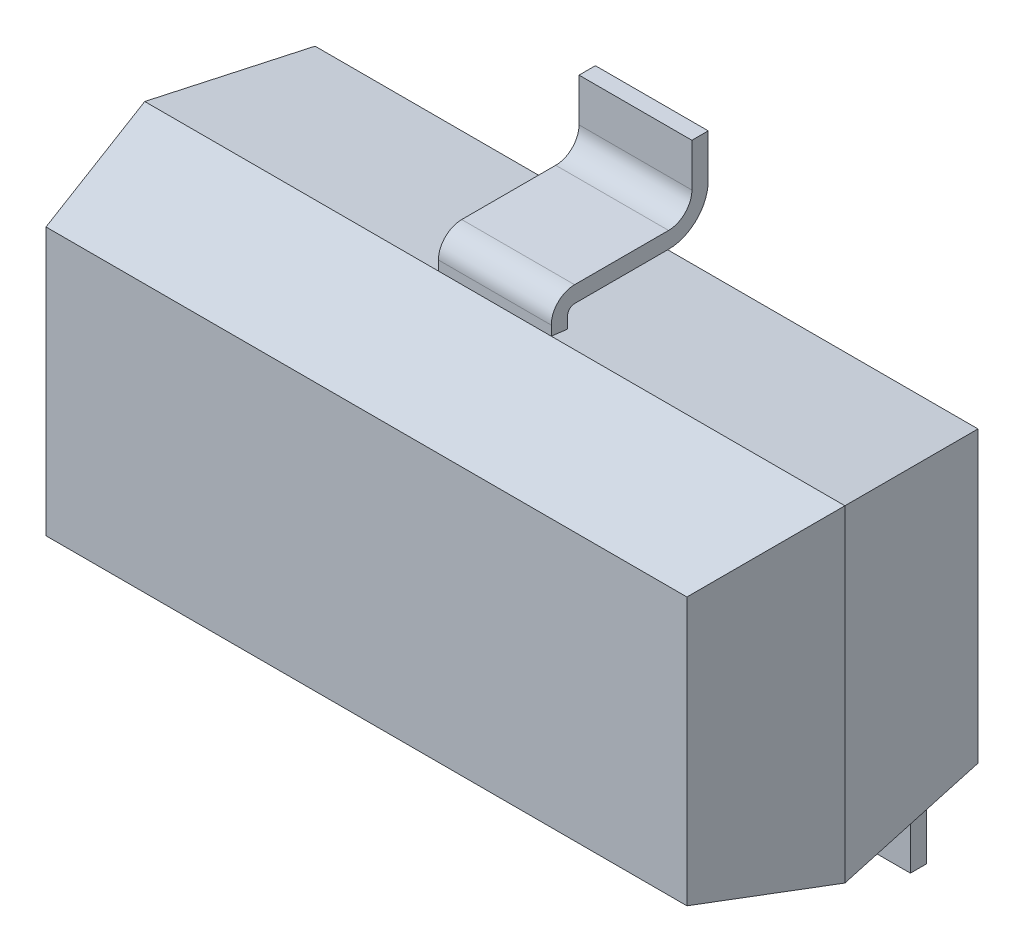
SolidWorks part; units mm, degrees
material "-"
ref_plane "Alzado" through (0, 0, 0) normal (0, 0, 1) x (1, 0, 0)
ref_plane "Planta" through (0, 0, 0) normal (0, 1, 0) x (1, 0, 0)
ref_plane "Vista lateral" through (0, 0, 0) normal (1, 0, 0) x (0, 0, -1)
sketch "Croquis1" plane through (0, 0, 0) normal (0, 0, 1) x (1, 0, 0)
  line L1 (1.5, 0.7) -> (-1.5, 0.7)
  line L2 (1.5, 0.7) -> (1.5, -0.7)
  line L3 (1.5, -0.7) -> (-1.5, -0.7)
  line L4 (-1.5, 0.7) -> (-1.5, -0.7)
  line L5 (1.5, 0.7) -> (-1.5, -0.7) construction
  line L6 (1.5, -0.7) -> (-1.5, 0.7) construction
  point P0 (0, 0)
  dimension "D1" = 1.4
  dimension "D2" = 3
extrude "Saliente-Extruir1" add sketch "Croquis1" along normal blind 0.55 draft 13 and the other way blind 0.65 draft 7
sketch "Croquis5" plane through (0, 0, 0) normal (0, 0, 1) x (1, 0, 0)
  line L0 (0, 1.2725) -> (0, 0) construction
  line L1 (0.6945, 0.573) -> (-0.7455, 0.573) construction
  line L2 (0, 0) -> (0, -1.0302) construction
  line L3 (0, -0.573) -> (-0.9362, -0.573) construction
  line L4 (-1.373, -0.573) -> (1.373, -0.573) construction
  line L5 (-0.9362, -0.573) -> (-0.9362, -1.0302) construction
  line L6 (-0.9362, -1.0302) -> (-0.6945, -1.0302) construction
  line L7 (-0.9362, -1.0302) -> (-1.178, -1.0302) construction
  line L8 (-1.178, -1.0302) -> (-1.178, -0.573) construction
  line L9 (-1.178, -0.573) -> (-0.6945, -0.573) construction
  line L10 (-0.6945, -0.573) -> (-0.6945, -1.0302) construction
  line L11 (-0.6945, -1.0302) -> (-0.6945, -0.573) construction
  line L12 (-0.9362, -0.573) -> (-0.9362, -1.1257) construction
  line L13 (-0.9362, -1.1257) -> (-0.6945, -1.1257) construction
  line L14 (-0.6945, -1.1257) -> (-0.6945, -1.0302) construction
  line L15 (-0.6945, -1.0302) -> (-1.178, -1.0302) construction
  line L16 (-1.178, -1.0302) -> (-1.178, -1.1257) construction
  line L17 (-1.178, -1.1257) -> (-0.9362, -1.1257) construction
  line L18 (-0.6945, -1.1257) -> (-0.6945, -0.7474) construction
  line L19 (-0.6945, -0.7474) -> (-1.178, -0.7474) construction
  line L20 (1.373, 0.573) -> (-1.373, 0.573) construction
  line L21 (-1.178, -0.573) -> (-0.6945, -0.573)
  line L23 (-0.6945, -0.573) -> (-0.6945, -1.1257)
  line L25 (-0.6945, -1.1257) -> (-1.178, -1.1257)
  line L26 (-1.178, -1.1257) -> (-1.178, -0.573)
  line L27 (1.178, -1.1257) -> (1.178, -0.573)
  line L28 (1.178, -0.573) -> (0.6945, -0.573)
  line L29 (0.6945, -0.573) -> (0.6945, -1.1257)
  line L30 (0.6945, -1.1257) -> (1.178, -1.1257)
  line L31 (0.2418, 0.573) -> (0.2418, 1.1257)
  line L32 (0.2418, 1.1257) -> (-0.2418, 1.1257)
  line L33 (-0.2418, 1.1257) -> (-0.2418, 0.573)
  line L34 (-0.2418, 0.573) -> (0.2418, 0.573)
  line L35 (-1.5, 0) -> (1.5, 0) construction
  line L36 (-1.5, 0.7) -> (-1.5, -0.7) construction
  line L37 (1.5, -0.7) -> (1.5, 0.7) construction
  dimension "D1" = 0.5527
extrude "Saliente-Extruir5" add sketch "Croquis5" against normal blind 0.69
sketch "Croquis7" plane through (-1.178, 0, 0) normal (-1, 0, 0) x (0, 0, 1)
  line L0 (-0.6026, -1.1257) -> (0, -1.1257)
  line L1 (-0.1, -0.8411) -> (-0.5026, -0.8411)
  line L2 (-0.6026, -0.9411) -> (-0.6026, -1.1257)
  line L3 (-0.07, -0.6914) -> (-0.07, -0.7411)
  line L4 (-0.1, -0.7711) -> (-0.5026, -0.7711)
  line L5 (0.55, 0) -> (-0.65, 0) construction
  line L6 (0, -1.1257) -> (0, -0.7)
  line L7 (0, -0.7) -> (-0.65, -0.6202)
  line L8 (-0.65, -0.6202) -> (-0.65, -0.573)
  line L9 (-0.65, -0.573) -> (-0.69, -0.573)
  line L10 (-0.69, -0.573) -> (-0.69, -1.1257)
  line L11 (-0.69, -1.1257) -> (0, -1.1257)
  line L12 (0, -1.1257) -> (0, -0.7411)
  line L13 (-0.07, -0.6914) -> (-0.65, -0.6202)
  line L14 (-0.65, -0.6202) -> (-0.65, -0.573)
  line L15 (-0.65, -0.573) -> (-0.69, -0.573)
  line L16 (-0.69, -0.573) -> (-0.69, -1.1257)
  line L17 (-0.69, -1.1257) -> (-0.6726, -1.1257)
  line L18 (-0.07, -0.7) -> (-0.07, -0.7411) construction
  line L19 (-0.6726, -0.9411) -> (-0.6726, -1.1257) construction
  line L20 (-0.6026, -0.9411) -> (-0.6026, -1.1257) construction
  line L21 (-0.6726, -0.9411) -> (-0.6726, -1.1257)
  line L22 (0, -0.7) -> (0, -0.7411) construction
  line L23 (0.55, -0.573) -> (0.55, 0.573) construction
  line L24 (-0.65, -0.6202) -> (-0.65, 0.6202) construction
  line L25 (-0.6726, 0.9411) -> (-0.6726, 1.1257)
  line L26 (-0.69, 1.1257) -> (-0.6726, 1.1257)
  line L27 (-0.69, 0.573) -> (-0.69, 1.1257)
  line L28 (-0.65, 0.573) -> (-0.69, 0.573)
  line L29 (-0.65, 0.6202) -> (-0.65, 0.573)
  line L30 (-0.07, 0.6914) -> (-0.65, 0.6202)
  line L31 (0, 1.1257) -> (0, 0.7411)
  line L32 (-0.1, 0.7711) -> (-0.5026, 0.7711)
  line L33 (-0.07, 0.6914) -> (-0.07, 0.7411)
  line L34 (-0.6026, 0.9411) -> (-0.6026, 1.1257)
  line L35 (-0.1, 0.8411) -> (-0.5026, 0.8411)
  line L36 (-0.6026, 1.1257) -> (0, 1.1257)
  arc A0 (-0.5026, -0.8411) -> (-0.6026, -0.9411) centre (-0.5026, -0.9411) ccw
  arc A1 (-0.1, -0.8411) -> (0, -0.7411) centre (-0.1, -0.7411) ccw
  arc A2 (-0.1, -0.7711) -> (-0.07, -0.7411) centre (-0.1, -0.7411) ccw
  arc A3 (-0.5026, -0.7711) -> (-0.6726, -0.9411) centre (-0.5026, -0.9411) ccw
  arc A4 (-0.5026, 0.7711) -> (-0.6726, 0.9411) centre (-0.5026, 0.9411) cw
  arc A5 (-0.1, 0.7711) -> (-0.07, 0.7411) centre (-0.1, 0.7411) cw
  arc A6 (-0.1, 0.8411) -> (0, 0.7411) centre (-0.1, 0.7411) cw
  arc A7 (-0.5026, 0.8411) -> (-0.6026, 0.9411) centre (-0.5026, 0.9411) cw
  point P13 (0, -0.8411)
  point P36 (0, 0.8411)
  dimension "D2" = 0.1
  dimension "D1" = 0
extrude "Cortar-Extruir2" cut sketch "Croquis7" against normal blind 2.69
